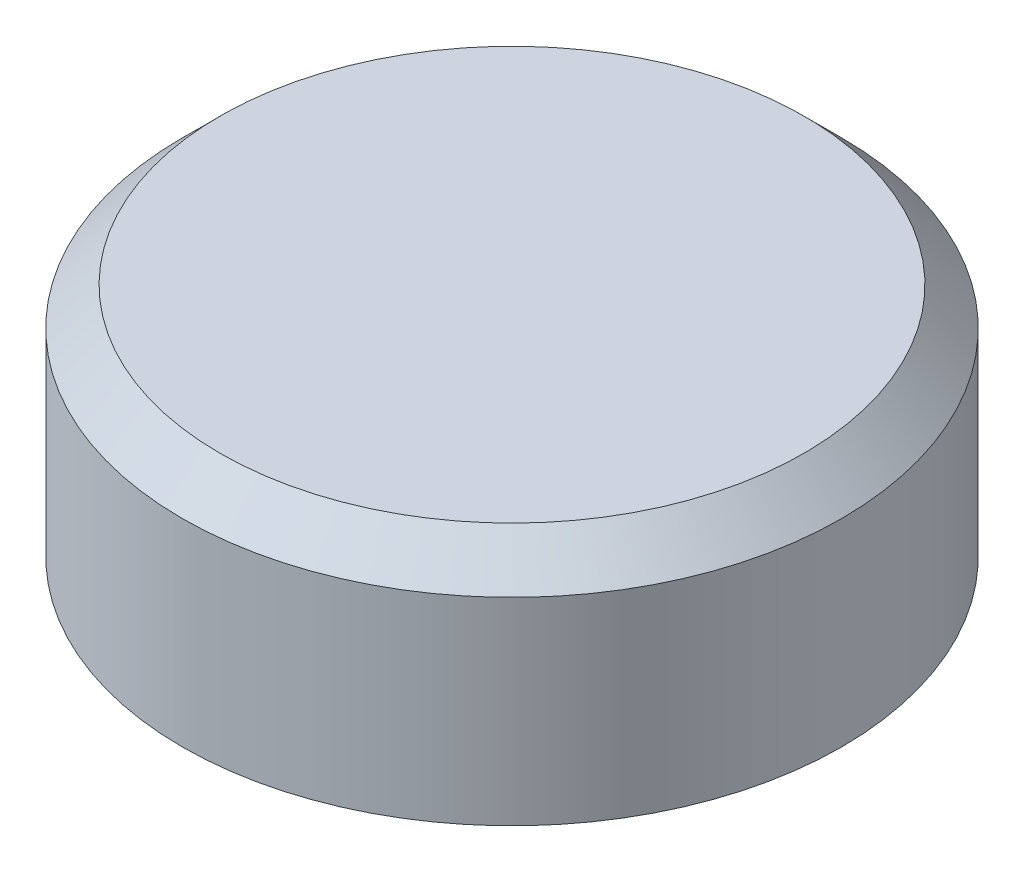
SolidWorks part; units mm, degrees
ref_plane "Front Plane" through (0, 0, 0) normal (0, 0, 1) x (1, 0, 0)
ref_plane "Top Plane" through (0, 0, 0) normal (0, 1, 0) x (1, 0, 0)
ref_plane "Right Plane" through (0, 0, 0) normal (1, 0, 0) x (0, 0, -1)
sketch "Sketch1" plane through (0, 0, 0) normal (0, 1, 0) x (1, 0, 0)
  circle A0 centre (0, 0) radius 17.5
  dimension "D1" = 35
extrude "Boss-Extrude1" add sketch "Sketch1" against normal blind 12.5
sketch "Sketch2" plane through (0, -12.5, 0) normal (0, -1, 0) x (1, 0, 0)
  circle A0 centre (0, 0) radius 15.9
  circle A1 centre (0, 0) radius 17.5 construction
  dimension "D1" = 1.6
extrude "Cut-Extrude1" cut sketch "Sketch2" against normal blind 11
chamfer "Chamfer1" distance 2 angle 45 1 edges at (0, 0, 17.5)
chamfer "Chamfer2" distance 2 angle 45 1 edges at (0, -1.5, -15.9)
